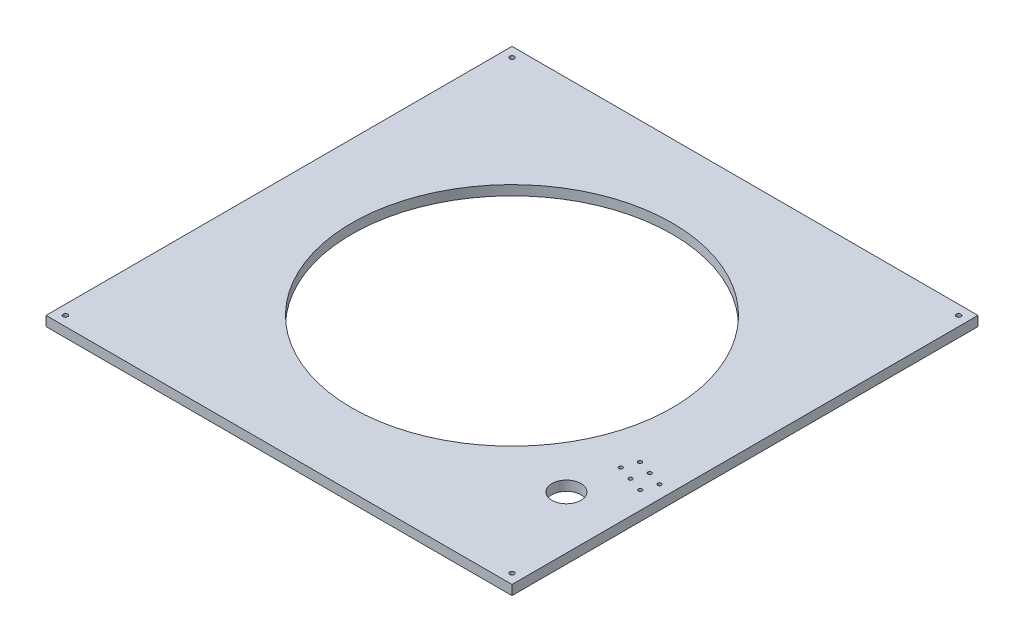
SolidWorks part; units mm, degrees
material "Pine"
ref_plane "Front Plane" through (0, 0, 0) normal (0, 0, 1) x (1, 0, 0)
ref_plane "Top Plane" through (0, 0, 0) normal (0, 1, 0) x (1, 0, 0)
ref_plane "Right Plane" through (0, 0, 0) normal (1, 0, 0) x (0, 0, -1)
sketch "Sketch1" plane through (0, 0, 0) normal (0, 1, 0) x (1, 0, 0)
  line L1 (-50.5057, 44.4593) -> (559.0943, 44.4593)
  line L2 (-50.5057, 44.4593) -> (-50.5057, -565.1407)
  line L3 (-50.5057, -565.1407) -> (559.0943, -565.1407)
  line L4 (559.0943, 44.4593) -> (559.0943, -565.1407)
  dimension "D1" = 609.6
  dimension "D2" = 609.6
extrude "Boss-Extrude1" add sketch "Sketch1" along normal blind 12.7
sketch "Sketch2" plane through (0, 12.7, 0) normal (0, 1, 0) x (1, 0, 0)
  line L0 (559.0943, 44.4593) -> (-50.5057, 44.4593) construction
  line L1 (-50.5057, 44.4593) -> (-50.5057, -565.1407) construction
  circle A0 centre (254.2943, -260.3407) radius 209.55
  dimension "D1" = 419.1
  dimension "D2" = 304.8
  dimension "D3" = 304.8
extrude "Cut-Extrude1" cut sketch "Sketch2" against normal through all
sketch "Sketch3" plane through (0, 0, 0) normal (0, -1, 0) x (1, 0, 0)
  line L0 (-50.5057, 565.1407) -> (559.0943, 565.1407) construction
  line L1 (559.0943, 565.1407) -> (559.0943, -44.4593) construction
  circle A0 centre (489.8943, 424.7407) radius 19
  dimension "D1" = 38
  dimension "D2" = 140.4
  dimension "D3" = 69.2
extrude "Cut-Extrude2" cut sketch "Sketch3" against normal through all
sketch "Sketch4" plane through (0, 12.7, 0) normal (0, 1, 0) x (1, 0, 0)
  line L0 (-50.5057, -565.1407) -> (559.0943, -565.1407) construction
  line L1 (559.0943, -565.1407) -> (559.0943, 44.4593) construction
  line L2 (542.0943, -355.1407) -> (504.0943, -342.6507) construction
  line L3 (541.9934, -365.6339) -> (496.2426, -350.5963) construction
  circle A0 centre (542.0943, -355.1407) radius 2.5
  circle A1 centre (523.0943, -348.8957) radius 2.5
  circle A2 centre (504.0943, -342.6507) radius 2.5
  circle A6 centre (497.8493, -361.6507) radius 2.5
  circle A7 centre (516.8493, -367.8957) radius 2.5
  circle A8 centre (535.8493, -374.1407) radius 2.5
  dimension "D1" = 210
  dimension "D5" = 5
  dimension "D6" = 5
  dimension "D7" = 5
  dimension "D2" = 17
  dimension "D3" = 55
  dimension "D4" = 20
  dimension "D11" = 10
  dimension "D12" = 20
  dimension "D13" = 40
  dimension "D14" = 10
extrude "Cut-Extrude3" cut sketch "Sketch4" against normal through all
sketch "Sketch5" plane through (0, 12.7, 0) normal (0, 1, 0) x (1, 0, 0)
  line L0 (-50.5057, -565.1407) -> (559.0943, -565.1407) construction
  line L1 (559.0943, -565.1407) -> (559.0943, 44.4593) construction
  line L2 (-50.5057, 44.4593) -> (-50.5057, -565.1407) construction
  line L3 (559.0943, 44.4593) -> (-50.5057, 44.4593) construction
  circle A0 centre (546.3943, -552.4407) radius 3
  circle A1 centre (-37.8057, -552.4407) radius 3
  circle A2 centre (-37.8057, 31.7593) radius 3
  circle A3 centre (546.3943, 31.7593) radius 3
  dimension "D1" = 12.7
  dimension "D2" = 12.7
  dimension "D3" = 12.7
  dimension "D4" = 12.7
  dimension "D5" = 12.7
  dimension "D7" = 12.7
  dimension "D9" = 6
  dimension "D10" = 6
  dimension "D11" = 6
  dimension "D12" = 6
  dimension "D6" = 12.7
  dimension "D8" = 12.7
extrude "Cut-Extrude4" cut sketch "Sketch5" against normal through all
